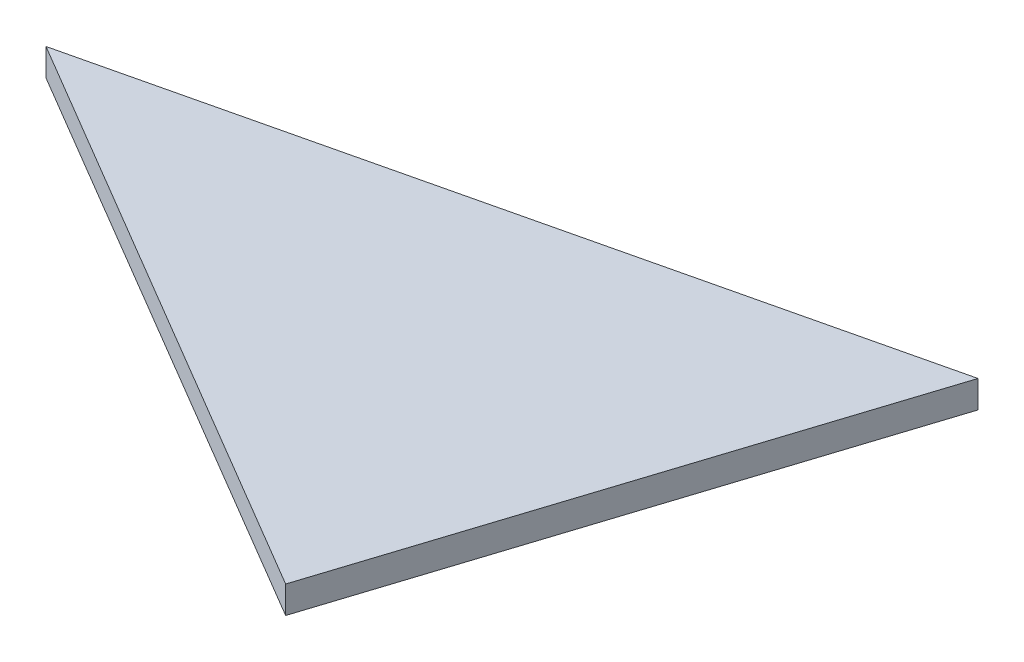
SolidWorks part; units mm, degrees
ref_plane "Plan de face" through (0, 0, 0) normal (0, 0, 1) x (1, 0, 0)
ref_plane "Plan de dessus" through (0, 0, 0) normal (0, 1, 0) x (1, 0, 0)
ref_plane "Plan de droite" through (0, 0, 0) normal (1, 0, 0) x (0, 0, -1)
sketch "Esquisse1" plane through (0, 0, 0) normal (0, 1, 0) x (1, 0, 0)
  line L0 (55.2443, 13.0873) -> (0, 0)
  line L1 (0, 0) -> (42.9151, -25.3443)
  line L2 (42.9151, -25.3443) -> (55.2443, 13.0873)
  point P3 (0, 0)
extrude "Boss.-Extru.1" add sketch "Esquisse1" along normal blind 2
